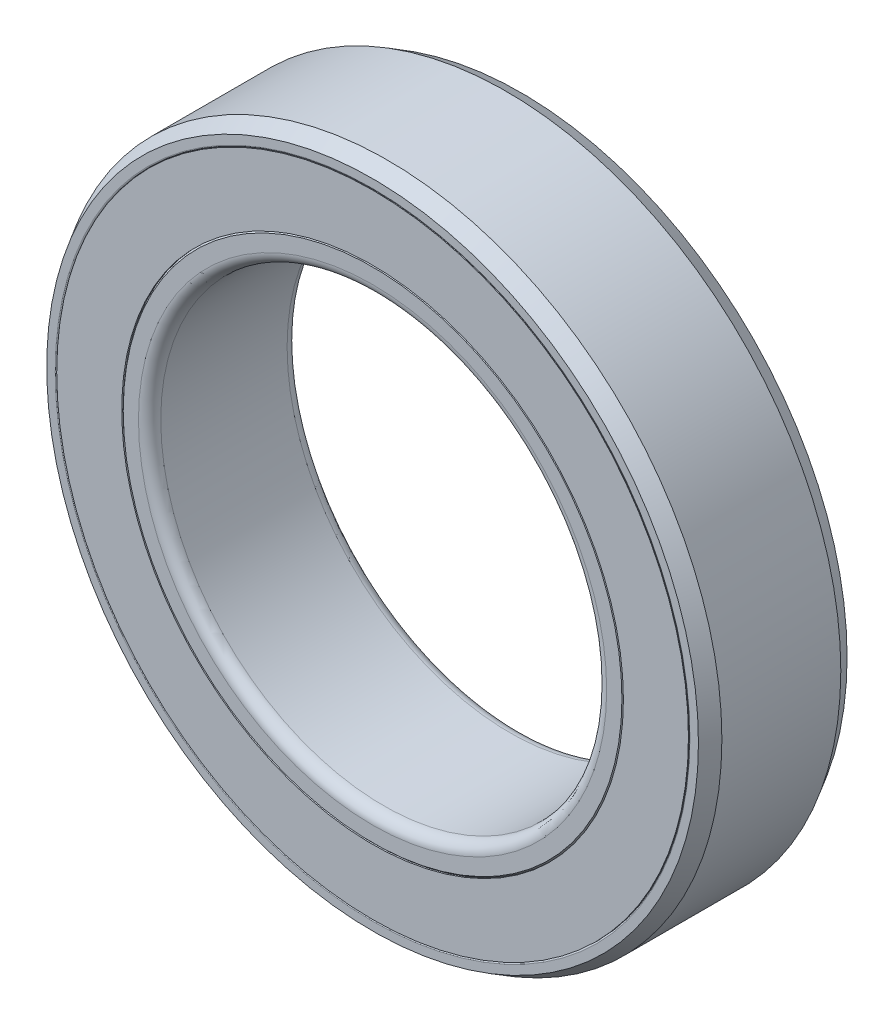
SolidWorks part; units mm, degrees
material "Alloy Steel"
ref_plane "Front Plane" through (0, 0, 0) normal (0, 0, 1) x (1, 0, 0)
ref_plane "Top Plane" through (0, 0, 0) normal (0, 1, 0) x (1, 0, 0)
ref_plane "Right Plane" through (0, 0, 0) normal (1, 0, 0) x (0, 0, -1)
sketch "Sketch1" plane through (0, 0, 0) normal (0, 0, 1) x (1, 0, 0)
  line L0 (0, 7.5) -> (0, 9) construction
  line L1 (0, 6) -> (0, 7.5) construction
  line L2 (0, 9) -> (0, 8.5) construction
  line L3 (0, 8.5) -> (0, 8) construction
  line L4 (0, 8) -> (0, 7.5) construction
  circle A0 centre (0, 0) radius 6
  circle A1 centre (0, 0) radius 9
  circle A2 centre (0, 0) radius 8.5 construction
  circle A4 centre (0, 0) radius 6.75 construction
  point P6 (0, 6.75)
  dimension "OD" = 18
  dimension "ID" = 12
sketch "Sketch2" plane through (0, 0, 0) normal (1, 0, 0) x (0, 0, -1)
  line L0 (-2, 9) -> (2, 9) construction
  line L1 (2, 9) -> (2, -9) construction
  line L2 (2, 0) -> (-2, 0) construction
  line L3 (-2, 6) -> (-2, -6) construction
  point P2 (0, 9)
  dimension "Width" = 4
  dimension "For Shaft Diameter" = 12
  dimension "For Housing ID" = 18
sketch "Sketch3" plane through (0, 0, 0) normal (1, 0, 0) x (0, 0, -1)
  line L0 (-1.6, -9) -> (1.6, -9)
  line L3 (-2, -8.54) -> (-2, -8.7691)
  line L4 (0, -6.75) -> (0, -8.5) construction
  line L5 (-1.6, -9) -> (-2, -8.7691)
  line L6 (-1.7, -6) -> (1.7, -6)
  line L7 (-0.8333, -8.5) -> (-0.8333, -8.6667) construction
  line L8 (-1.96, -6.75) -> (-0.8333, -6.75)
  line L9 (-2, -6.75) -> (0, -6.75) construction
  line L11 (-2, -8.5) -> (-2, -6.75) construction
  line L12 (-2, -6.71) -> (-2, -6.3)
  line L14 (-2, 0) -> (2, 0) construction
  line L15 (-1.96, -8.5) -> (-0.8333, -8.5)
  line L17 (0, 0) -> (0, -9) construction
  line L18 (-0.8333, -8.6667) -> (-0.8333, -8.8333) construction
  line L19 (1.6, -9) -> (2, -8.7691)
  line L20 (0, -8.5) -> (-2, -8.5) construction
  line L21 (-2, 6) -> (-2, -6) construction
  line L22 (-0.8333, -8.8333) -> (-0.8333, -9) construction
  line L30 (-2, -6.71) -> (-1.96, -6.75)
  line L31 (1.96, -6.75) -> (0.8333, -6.75)
  line L32 (2, -6.71) -> (1.96, -6.75)
  line L33 (2, -6.71) -> (2, -6.3)
  line L34 (1.96, -8.5) -> (0.8333, -8.5)
  line L35 (2, -8.54) -> (2, -8.7691)
  line L36 (0, 9) -> (0, -9) construction
  arc A0 (0, -6.4167) -> (0, -8.8333) centre (0, -7.625) ccw construction
  arc A1 (-0.8333, -6.75) -> (0.8333, -6.75) centre (0, -7.625) cw
  arc A2 (-0.8333, -8.5) -> (0.8333, -8.5) centre (0, -7.625) ccw
  arc A4 (-1.96, -8.5) -> (-2, -8.54) centre (-1.96, -8.54) ccw
  arc A5 (-1.7, -6) -> (-2, -6.3) centre (-1.7, -6.3) ccw
  arc A6 (1.7, -6) -> (2, -6.3) centre (1.7, -6.3) cw
  arc A7 (1.96, -8.5) -> (2, -8.54) centre (1.96, -8.54) cw
  point P28 (0, -7.625)
  point P46 (-2, -6)
  point P54 (0, -6)
  dimension "D4" = 0.04
  dimension "D7" = 0.3
  dimension "D5" = 45
  dimension "D6" = 0.04
  dimension "D3" = 0.4
  dimension "D2" = 60
revolve "Revolve1" add sketch "Sketch3" angle 360 about L14
sketch "Sketch4" plane through (0, 0, 0) normal (1, 0, 0) x (0, 0, -1)
  line L0 (-1.96, -8.5) -> (-0.8333, -8.5) construction
  line L1 (-2, -6.75) -> (-1.4063, -6.75)
  line L2 (-2, -6.75) -> (-2, -8.5)
  line L3 (-2, -8.5) -> (-1.4063, -8.5)
  line L4 (-1.4063, -6.75) -> (-1.4063, -8.5)
  line L5 (-2, -6.71) -> (-2, -6.3) construction
  line L6 (-2, -7.625) -> (-1.8021, -7.625) construction
  line L7 (-1.8021, -7.625) -> (-1.6042, -7.625) construction
  line L8 (-1.6042, -7.625) -> (-1.4063, -7.625) construction
  line L9 (-1.4063, -7.625) -> (-1.2083, -7.625) construction
  line L10 (-2, -8.5) -> (-2, -6.75) construction
  line L11 (-1.96, -6.75) -> (-0.8333, -6.75) construction
  arc A1 (0, -6.4167) -> (0, -8.8333) centre (0, -7.625) ccw construction
revolve "Revolve2" add sketch "Sketch4" angle 360 about L14
sketch "Sketch5" plane through (0, 0, 0) normal (1, 0, 0) x (0, 0, -1)
  line L2 (0, -6.4167) -> (0, -8.8333)
  arc A2 (0, -8.8333) -> (0, -6.4167) centre (0, -7.625) cw
revolve "Revolve3" add sketch "Sketch5" angle 360 about L17
pattern_circular "CirPattern1" count 7 over 360 about axis through (0, 0, 0) along (0, 0, 1) of bodies 138
equation "\"D4@Sketch3\"=\"Width@Sketch2\"*.01"
equation "\"D6@Sketch3\"=\"Width@Sketch2\"*.01"
equation "\"D7@Sketch3\"=\"Width@Sketch2\"*.075"
equation "\"D3@Sketch3\"=\"Width@Sketch2\"*.1"
